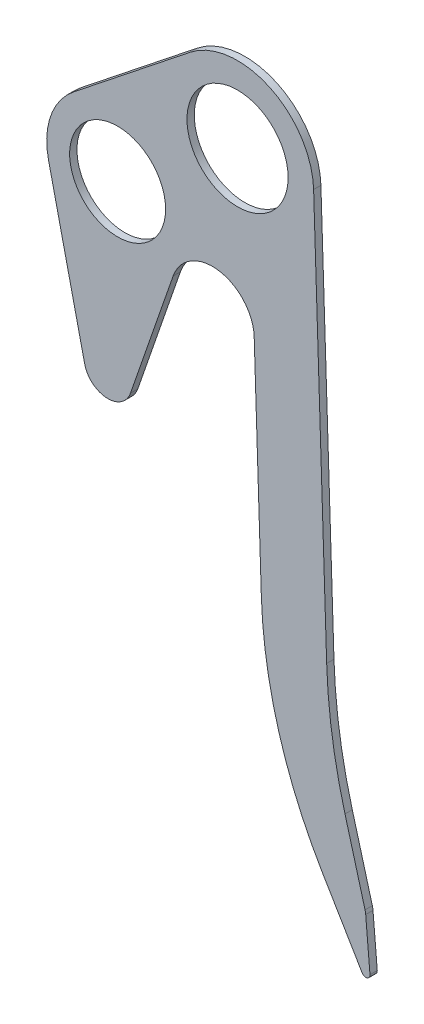
SolidWorks part; units mm, degrees
ref_plane "Plane1" through (0, 0, 0) normal (0, 0, 1) x (1, 0, 0)
ref_plane "Plane2" through (0, 0, 0) normal (0, 1, 0) x (1, 0, 0)
ref_plane "Plane3" through (0, 0, 0) normal (1, 0, 0) x (0, 0, -1)
sketch "Sketch1" plane through (0, 0, 0) normal (0, 0, 1) x (1, 0, 0)
  line L0 (-181.297, -100.1232) -> (-146.6054, -252.2042)
  line L1 (-45.4166, 57.1518) -> (-157.3059, -31.7627)
  line L2 (72.962, 2.3567) -> (85.4735, -385)
  line L3 (15.9792, -148.7087) -> (22.8038, -360)
  line L4 (81.4729, -560.9129) -> (119.5608, -625.0426)
  line L5 (-61.7865, -136.8783) -> (-102.674, -254.6219)
  line L6 (122.2692, -571.2311) -> (103.0495, -501.2159)
  line L7 (0, 0) -> (320.0502, 0) construction
  line L8 (126.9856, -622.6605) -> (122.9105, -574.8277)
  line L9 (0, 0) -> (0, -638.1642) construction
  circle A0 centre (0, 0) radius 48.5
  circle A1 centre (-115, -85) radius 46
  arc A2 (-157.3059, -31.7627) -> (-181.297, -100.1232) centre (-115, -85) ccw
  arc A3 (72.962, 2.3567) -> (-45.4166, 57.1518) centre (0, 0) ccw
  arc A4 (22.8038, -360) -> (81.4729, -560.9129) centre (442.5849, -346.4411) ccw
  arc A5 (15.9792, -148.7087) -> (-61.7865, -136.8783) centre (-24, -150) ccw
  arc A6 (-146.6054, -252.2042) -> (-102.674, -254.6219) centre (-124.2931, -247.1145) ccw
  arc A7 (119.5608, -625.0426) -> (126.9856, -622.6605) centre (123, -623) ccw
  arc A8 (122.9105, -574.8277) -> (122.2692, -571.2311) centre (102.9827, -576.5254) ccw
  arc A9 (103.0495, -501.2159) -> (85.4735, -385) centre (585.2129, -368.8585) cw
  point P30 (122.7548, -573)
  dimension "D4" = 22.8855
  dimension "D5" = 24
  dimension "D7" = 40
  dimension "D8" = 68
  dimension "D9" = 73
  dimension "D12" = 270
  dimension "D15" = 97
  dimension "D16" = 92
  dimension "D17" = 123
  dimension "D19" = 61.8299
  dimension "D11" = 4
  dimension "D22" = 420
  dimension "D23" = 500
  dimension "D25" = 20
  dimension "D1" = 115
  dimension "D2" = 85
  dimension "D3" = 32
  dimension "D6" = 385
  dimension "D10" = 12.85
  dimension "D13" = 623
  dimension "D14" = 15.35
  dimension "D18" = 88.15
  dimension "D20" = 150
  dimension "D21" = 50
  dimension "D24" = 360
extrude "Extrude1" add sketch "Sketch1" along normal blind 7
